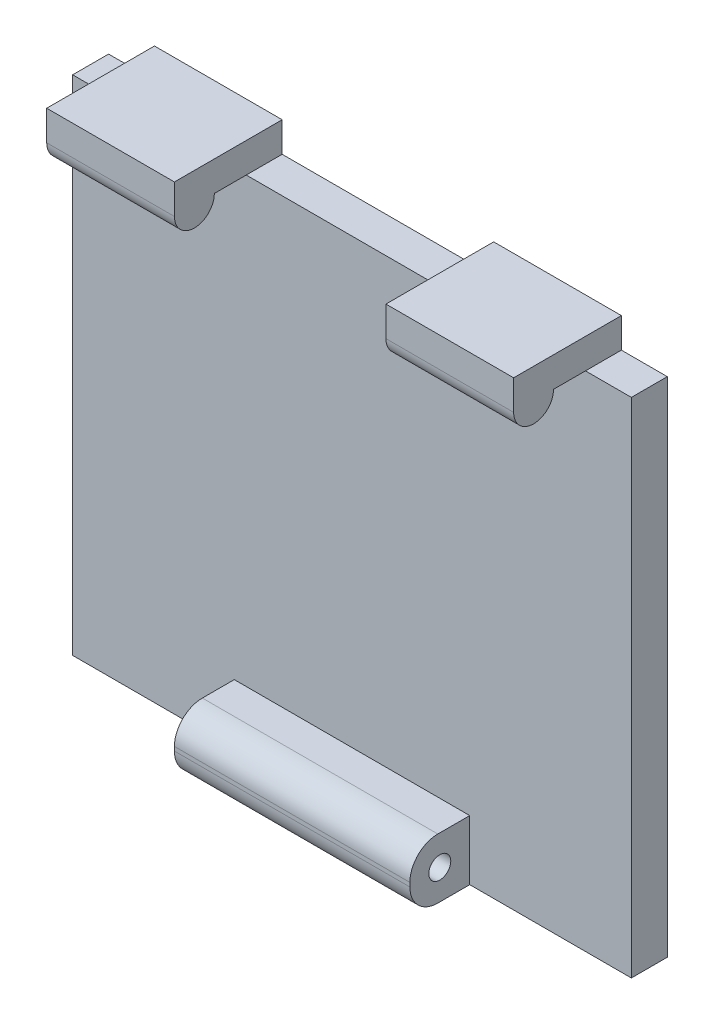
SolidWorks part; units mm, degrees
ref_plane "Front" through (0, 0, 0) normal (0, 0, 1) x (1, 0, 0)
ref_plane "Top" through (0, 0, 0) normal (0, 1, 0) x (1, 0, 0)
ref_plane "Right" through (0, 0, 0) normal (1, 0, 0) x (0, 0, -1)
sketch "草图1" plane through (0, 0, 0) normal (0, 0, 1) x (1, 0, 0)
  line L1 (0, 0) -> (28, 0)
  line L2 (0, 0) -> (0, -25.2)
  line L3 (0, -25.2) -> (28, -25.2)
  line L4 (28, 0) -> (28, -25.2)
  dimension "D1" = 28
  dimension "D2" = 25.2
extrude "凸台-拉伸1" add sketch "草图1" along normal blind 1.8
sketch "草图2" plane through (0, 0, 1.8) normal (0, 0, 1) x (1, 0, 0)
  line L0 (0, -25.2) -> (28, -25.2) construction
  line L1 (8.1, -25.2) -> (19.9, -25.2)
  line L2 (8.1, -25.2) -> (8.1, -22.2)
  line L3 (8.1, -22.2) -> (19.9, -22.2)
  line L4 (19.9, -25.2) -> (19.9, -22.2)
  line L5 (0, 0) -> (0, -25.2) construction
  dimension "D1" = 11.8
  dimension "D2" = 8.1
  dimension "D3" = 3
extrude "凸台-拉伸2" add sketch "草图2" along normal blind 3
fillet "圆角1" radius 1.4 2 edges at (14, -22.2, 4.8) (14, -25.2, 4.8)
sketch "草图3" plane through (19.9, 0, 0) normal (1, 0, 0) x (0, 0, -1)
  line L0 (-3.4, -25.2) -> (-1.8, -25.2) construction
  line L2 (-1.8, -25.2) -> (-1.8, -22.2) construction
  circle A0 centre (-3.3, -23.7) radius 0.55
  dimension "D1" = 1.1
  dimension "D2" = 1.5
  dimension "D3" = 1.5
extrude "切除-拉伸1" cut sketch "草图3" against normal through all
sketch "草图4" plane through (0, 0, 0) normal (0, 1, 0) x (1, 0, 0)
  line L0 (28, 0) -> (0, 0) construction
  line L1 (2.3, 0) -> (8.7, 0)
  line L2 (2.3, 0) -> (2.3, -1.8)
  line L3 (2.3, -1.8) -> (8.7, -1.8)
  line L4 (8.7, 0) -> (8.7, -1.8)
  line L5 (28, -1.8) -> (0, -1.8) construction
  line L6 (0, -1.8) -> (0, 0) construction
  line L7 (28, -1.8) -> (28, 0) construction
  line L8 (19.3, 0) -> (25.7, 0)
  line L9 (19.3, 0) -> (19.3, -1.8)
  line L10 (19.3, -1.8) -> (25.7, -1.8)
  line L11 (25.7, 0) -> (25.7, -1.8)
  dimension "D1" = 6.4
  dimension "D2" = 6.4
  dimension "D3" = 2.3
  dimension "D4" = 2.3
extrude "凸台-拉伸3" add sketch "草图4" along normal blind 1.5
sketch "草图5" plane through (0, 0, 1.8) normal (0, 0, 1) x (1, 0, 0)
  line L1 (2.3, 1.5) -> (8.7, 1.5)
  line L2 (2.3, 1.5) -> (2.3, 0)
  line L3 (2.3, 0) -> (8.7, 0)
  line L4 (8.7, 1.5) -> (8.7, 0)
  line L5 (19.3, 1.5) -> (25.7, 1.5)
  line L6 (19.3, 1.5) -> (19.3, 0)
  line L7 (19.3, 0) -> (25.7, 0)
  line L8 (25.7, 1.5) -> (25.7, 0)
extrude "凸台-拉伸4" add sketch "草图5" along normal blind 3.6
sketch "草图7" plane through (25.7, 0, 0) normal (1, 0, 0) x (0, 0, -1)
  line L0 (-5.4, 0) -> (-1.8, 0) construction
  circle A0 centre (-4.4, 0) radius 1
  dimension "D1" = 2
extrude "凸台-拉伸5" add sketch "草图7" against normal blind 6.4
sketch "草图8" plane through (2.3, 0, 0) normal (-1, 0, 0) x (0, 0, 1)
  line L0 (5.4, 0) -> (1.8, 0) construction
  circle A0 centre (4.4, 0) radius 1
  dimension "D1" = 2
extrude "凸台-拉伸6" add sketch "草图8" against normal blind 6.4
